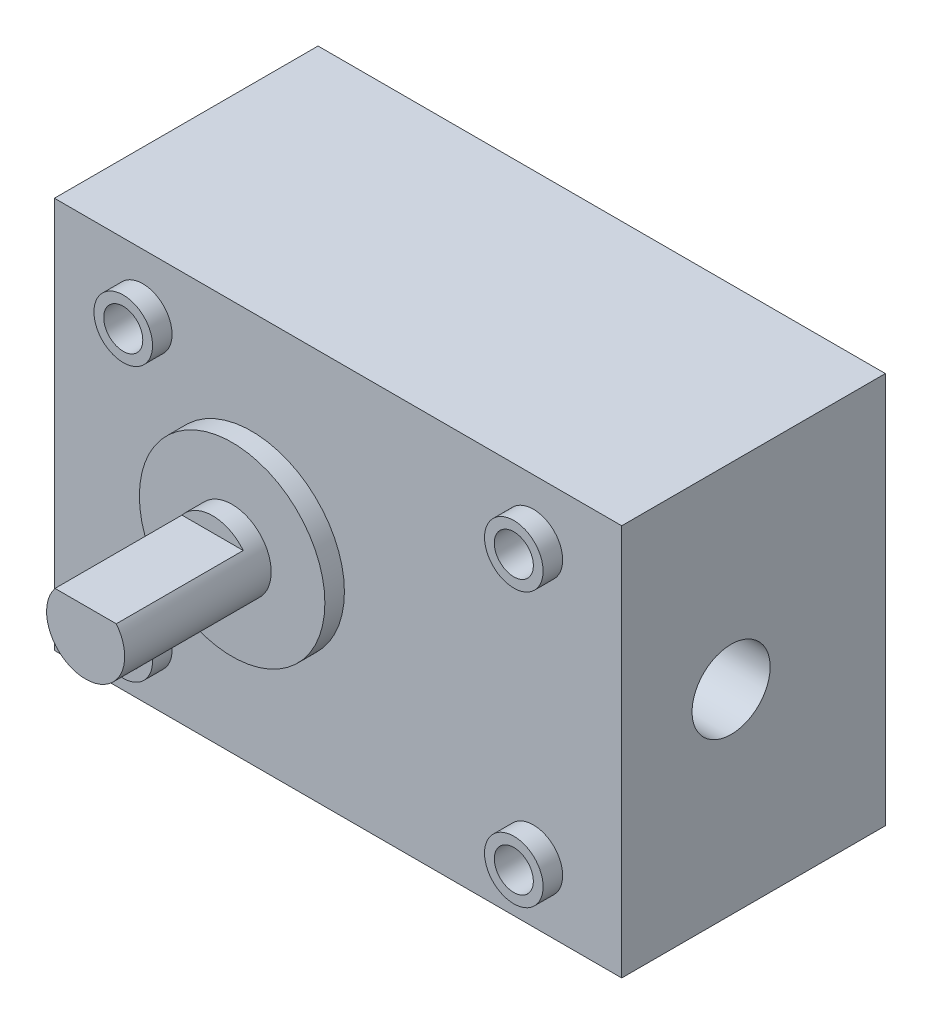
SolidWorks part; units mm, degrees
ref_plane "Front Plane" through (0, 0, 0) normal (0, 0, 1) x (1, 0, 0)
ref_plane "Top Plane" through (0, 0, 0) normal (0, 1, 0) x (1, 0, 0)
ref_plane "Right Plane" through (0, 0, 0) normal (1, 0, 0) x (0, 0, -1)
sketch "Sketch1" plane through (0, 0, 0) normal (0, 0, 1) x (1, 0, 0)
  line L1 (0, 0) -> (58.1, 0)
  line L2 (0, 0) -> (0, 40.11)
  line L3 (0, 40.11) -> (58.1, 40.11)
  line L4 (58.1, 0) -> (58.1, 40.11)
  dimension "D1" = 40.11
  dimension "D2" = 58.1
extrude "Boss-Extrude1" add sketch "Sketch1" along normal blind 27
sketch "Sketch2" plane through (0, 0, 27) normal (0, 0, 1) x (1, 0, 0)
  line L0 (58.1, 0) -> (58.1, 40.11) construction
  circle A0 centre (20.2, 20.055) radius 9.5
  point P4 (0, 0)
  dimension "D1" = 19
  dimension "D2" = 37.9
extrude "Boss-Extrude2" add sketch "Sketch2" along normal blind 2
sketch "Sketch3" plane through (0, 0, 29) normal (0, 0, 1) x (1, 0, 0)
  circle A0 centre (20.2, 20.055) radius 4
  dimension "D1" = 8
extrude "Boss-Extrude3" add sketch "Sketch3" along normal blind 15
sketch "Sketch4" plane through (0, 0, 44) normal (0, 0, 1) x (1, 0, 0)
  line L0 (17.0616, 22.535) -> (23.3384, 22.535)
  line L1 (23.3384, 22.535) -> (23.3384, 24.5338)
  line L2 (23.3384, 24.5338) -> (17.0616, 24.5338)
  line L3 (17.0616, 24.5338) -> (17.0616, 22.535)
  circle A0 centre (20.2, 20.055) radius 4 construction
extrude "Cut-Extrude1" cut sketch "Sketch4" against normal blind 13
sketch "Sketch5" plane through (0, 0, 27) normal (0, 0, 1) x (1, 0, 0)
  line L0 (29.05, 40.11) -> (29.05, 0) construction
  line L1 (58.1, 40.11) -> (0, 40.11) construction
  line L2 (0, 0) -> (58.1, 0) construction
  line L3 (0, 20.055) -> (58.1, 20.055) construction
  line L4 (0, 40.11) -> (0, 0) construction
  line L5 (58.1, 0) -> (58.1, 40.11) construction
  circle A0 centre (9.05, 34.055) radius 3
  circle A2 centre (49.05, 34.055) radius 3
  circle A3 centre (49.05, 6.055) radius 3
  circle A4 centre (9.05, 6.055) radius 3
  dimension "D3" = 6
  dimension "D1" = 20
  dimension "D2" = 14
extrude "Boss-Extrude4" add sketch "Sketch5" along normal blind 2
sketch "Sketch6" plane through (0, 0, 29) normal (0, 0, 1) x (1, 0, 0)
  circle A0 centre (9.05, 34.055) radius 2
  circle A1 centre (49.05, 34.055) radius 2
  circle A2 centre (49.05, 6.055) radius 2
  circle A3 centre (9.05, 6.055) radius 2
  dimension "D1" = 4
extrude "Cut-Extrude2" cut sketch "Sketch6" against normal blind 8
sketch "Sketch7" plane through (58.1, 0, 0) normal (1, 0, 0) x (0, 0, -1)
  line L0 (-27, 0) -> (0, 0) construction
  line L1 (-27, 0) -> (-27, 40.11) construction
  circle A0 centre (-15.7979, 20) radius 4
  dimension "D1" = 8
  dimension "D2" = 20
  dimension "D3" = 11.2021
extrude "Cut-Extrude3" cut sketch "Sketch7" against normal blind 25.4
